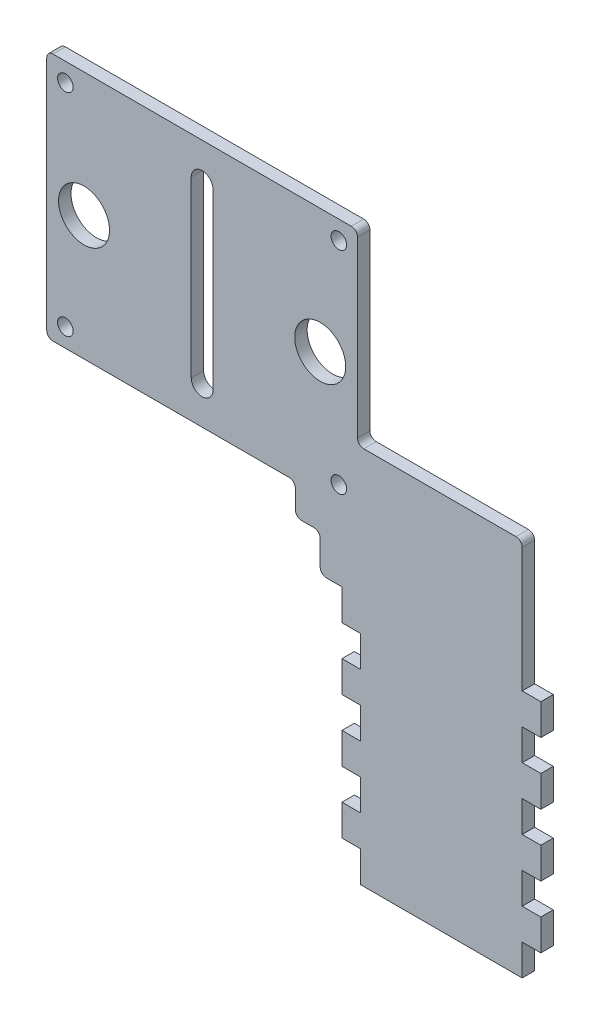
SolidWorks part; units mm, degrees
ref_plane "Front Plane" through (0, 0, 0) normal (0, 0, 1) x (1, 0, 0)
ref_plane "Top Plane" through (0, 0, 0) normal (0, 1, 0) x (1, 0, 0)
ref_plane "Right Plane" through (0, 0, 0) normal (1, 0, 0) x (0, 0, -1)
sketch "Sketch1" plane through (0, 0, 0) normal (0, 0, 1) x (1, 0, 0)
  line L1 (0, 0) -> (50, 0)
  line L2 (0, 0) -> (0, 40)
  line L3 (0, 40) -> (50, 40)
  line L4 (50, 0) -> (50, 40)
  line L5 (50, 0) -> (76.5, 0)
  line L6 (50, 0) -> (50, -51)
  line L7 (50, -51) -> (76.5, -51)
  line L8 (76.5, 0) -> (76.5, -51)
  line L9 (50, 0) -> (76.5, 0)
  line L12 (76.5, 0) -> (76.5, -21)
  line L13 (76.5, 0) -> (50, 0)
  line L14 (76.5, 0) -> (76.5, 10)
  line L15 (76.5, 10) -> (50, 10)
  line L16 (50, 0) -> (50, 10)
  line L17 (40, 0) -> (50, 0)
  line L18 (40, 0) -> (40, -5)
  line L19 (40, -5) -> (50, -5)
  line L20 (50, 0) -> (50, -5)
  line L21 (50, -5) -> (44, -5)
  line L22 (50, -5) -> (50, -11)
  line L23 (50, -11) -> (44, -11)
  line L24 (44, -5) -> (44, -11)
  dimension "D1" = 50
  dimension "D2" = 40
  dimension "D3" = 26.5
  dimension "D4" = 51
  dimension "D5" = 0
  dimension "D6" = 10
  dimension "D7" = 0
  dimension "D8" = 0
  dimension "D9" = 0
  dimension "D10" = 10
  dimension "D11" = 5
  dimension "D12" = 0
  dimension "D13" = 0
  dimension "D14" = 6
  dimension "D15" = 6
extrude "plate_body" add sketch "Sketch1" along normal blind 2 contours L1 L4 L3 L2 | L8 L5 L1 L6 L7 | L14 L15 L4 L5 | L18 L19 L6 L1 | L19 L24 L23 L6
sketch "Sketch2" plane through (0, 0, 2) normal (0, 0, 1) x (1, 0, 0)
  line L2 (0, 0) -> (0, 40) construction
  line L3 (0, 40) -> (50, 40) construction
  circle A0 centre (6, 20) radius 4.1
  circle A1 centre (44, 20) radius 4.1
  dimension "D1" = 38
  dimension "D2" = 8.2
  dimension "D3" = 8.2
  dimension "D4" = 6
  dimension "D5" = 20
  dimension "D6" = 20
extrude "shaft_bearings" cut sketch "Sketch2" against normal through all
sketch "Sketch4" plane through (0, 0, 2) normal (0, 0, 1) x (1, 0, 0)
  line L0 (25, 34) -> (25, 6) construction
  line L1 (26.75, 34) -> (26.75, 6)
  line L2 (23.25, 34) -> (23.25, 6)
  line L3 (0, 0) -> (40, 0) construction
  line L5 (0, 0) -> (0, 40) construction
  arc A0 (26.75, 34) -> (23.25, 34) centre (25, 34) ccw
  arc A1 (23.25, 6) -> (26.75, 6) centre (25, 6) ccw
  point P2 (25, 20)
  dimension "D4" = 6
  dimension "D1" = 3.5
  dimension "D2" = 28
  dimension "D3" = 25
extrude "slot" cut sketch "Sketch4" against normal through all
sketch "Sketch5" plane through (0, 0, 2) normal (0, 0, 1) x (1, 0, 0)
  line L0 (0, 40) -> (50, 40) construction
  line L1 (0, 0) -> (0, 40) construction
  line L3 (50, 10) -> (50, 40) construction
  line L4 (0, 0) -> (40, 0) construction
  circle A0 centre (3, 37) radius 1.25
  circle A1 centre (47, 37) radius 1.25
  circle A2 centre (3, 3) radius 1.25
  circle A3 centre (47, 3) radius 1.25
  dimension "D1" = 2.5
  dimension "D2" = 2.5
  dimension "D3" = 2.5
  dimension "D4" = 2.5
  dimension "D5" = 3
  dimension "D6" = 3
  dimension "D7" = 3
  dimension "D8" = 3
  dimension "D9" = 3
  dimension "D10" = 3
  dimension "D11" = 3
  dimension "D12" = 3
extrude "bolt_holes" cut sketch "Sketch5" against normal through all
sketch "Sketch6" plane through (0, 0, 2) normal (0, 0, 1) x (1, 0, 0)
  line L0 (50, -51) -> (76.5, -51) construction
  line L1 (50, -11) -> (50.5, -11)
  line L2 (50, -11) -> (50, -51)
  line L3 (50, -51) -> (50.5, -51)
  line L4 (50.5, -11) -> (50.5, -51)
  line L5 (50, -11) -> (44, -11) construction
  dimension "D1" = 0.5
  dimension "D2" = 0
extrude "Cut-Extrude1" cut sketch "Sketch6" against normal through all
sketch "Sketch8" plane through (0, 0, 2) normal (0, 0, 1) x (1, 0, 0)
  line L0 (50.5, -36) -> (47.5, -36)
  line L1 (50.5, -46) -> (47.5, -46)
  line L2 (50.5, -46) -> (50.5, -41)
  line L3 (50.5, -41) -> (47.5, -41)
  line L4 (47.5, -46) -> (47.5, -41)
  line L5 (76.5, -46) -> (79.5, -46)
  line L6 (76.5, -46) -> (76.5, -41)
  line L7 (76.5, -41) -> (79.5, -41)
  line L8 (79.5, -46) -> (79.5, -41)
  line L9 (50.5, -36) -> (50.5, -31)
  line L10 (50.5, -31) -> (47.5, -31)
  line L11 (47.5, -36) -> (47.5, -31)
  line L12 (76.5, -36) -> (79.5, -36)
  line L13 (76.5, -36) -> (76.5, -31)
  line L14 (76.5, -31) -> (79.5, -31)
  line L15 (79.5, -36) -> (79.5, -31)
  line L16 (50.5, -51) -> (50.5, -11) construction
  line L17 (76.5, -51) -> (76.5, 10) construction
  line L18 (50.5, -16) -> (47.5, -16)
  line L19 (50.5, -26) -> (47.5, -26)
  line L20 (50.5, -26) -> (50.5, -21)
  line L21 (50.5, -21) -> (47.5, -21)
  line L22 (47.5, -26) -> (47.5, -21)
  line L23 (76.5, -26) -> (79.5, -26)
  line L24 (76.5, -26) -> (76.5, -21)
  line L25 (76.5, -21) -> (79.5, -21)
  line L26 (79.5, -26) -> (79.5, -21)
  line L27 (50.5, -16) -> (50.5, -11)
  line L28 (50.5, -11) -> (47.5, -11)
  line L29 (47.5, -16) -> (47.5, -11)
  line L30 (76.5, -16) -> (79.5, -16)
  line L31 (76.5, -16) -> (76.5, -11)
  line L32 (76.5, -11) -> (79.5, -11)
  line L33 (79.5, -16) -> (79.5, -11)
  line L34 (50.5, -51) -> (76.5, -51) construction
  point P38 (78, -31)
  point P41 (78, -41)
  dimension "D1" = 5
  dimension "D2" = 5
  dimension "D3" = 3
  dimension "D4" = 3
  dimension "D5" = 5
  dimension "D6" = 5
  dimension "D7" = 3
  dimension "D8" = 3
  dimension "D9" = 0
  dimension "D10" = 0
  dimension "D11" = 5
  dimension "D12" = 5
  dimension "D13" = 5
  dimension "D14" = 5
  dimension "D15" = 3
  dimension "D16" = 3
  dimension "D17" = 5
  dimension "D18" = 5
  dimension "D19" = 3
  dimension "D20" = 3
  dimension "D21" = 5
  dimension "D22" = 5
  dimension "D25" = 0
  dimension "D26" = 0
  dimension "D27" = 5
  dimension "D28" = 5
  dimension "D29" = 10
  dimension "D30" = 10
extrude "finger_joints" add sketch "Sketch8" along direction (0, 0, 1) on the side against the normal up to surface (2 mm away)
sketch "Sketch9" plane through (0, 0, 2) normal (0, 0, 1) x (1, 0, 0)
  line L0 (50.5, -51) -> (76.5, -51) construction
  line L1 (55.5, -23) -> (63.5, -23)
  line L2 (55.5, -23) -> (55.5, -39)
  line L3 (55.5, -39) -> (63.5, -39)
  line L4 (63.5, -23) -> (63.5, -39)
  line L5 (50.5, -51) -> (50.5, -46) construction
  dimension "D1" = 8
  dimension "D2" = 16
  dimension "D3" = 12
  dimension "D4" = 5
extrude "Cut-Extrude2" [suppressed] cut sketch "Sketch9" against normal through all
fillet "1mm_fillets" radius 1 9 edges at (44, -11, 1) (44, -5, 1) (40, -5, 1) (40, 0, 1) (0, 0, 1) (0, 40, 1) (50, 40, 1) (50, 10, 1) (76.5, 10, 1)
